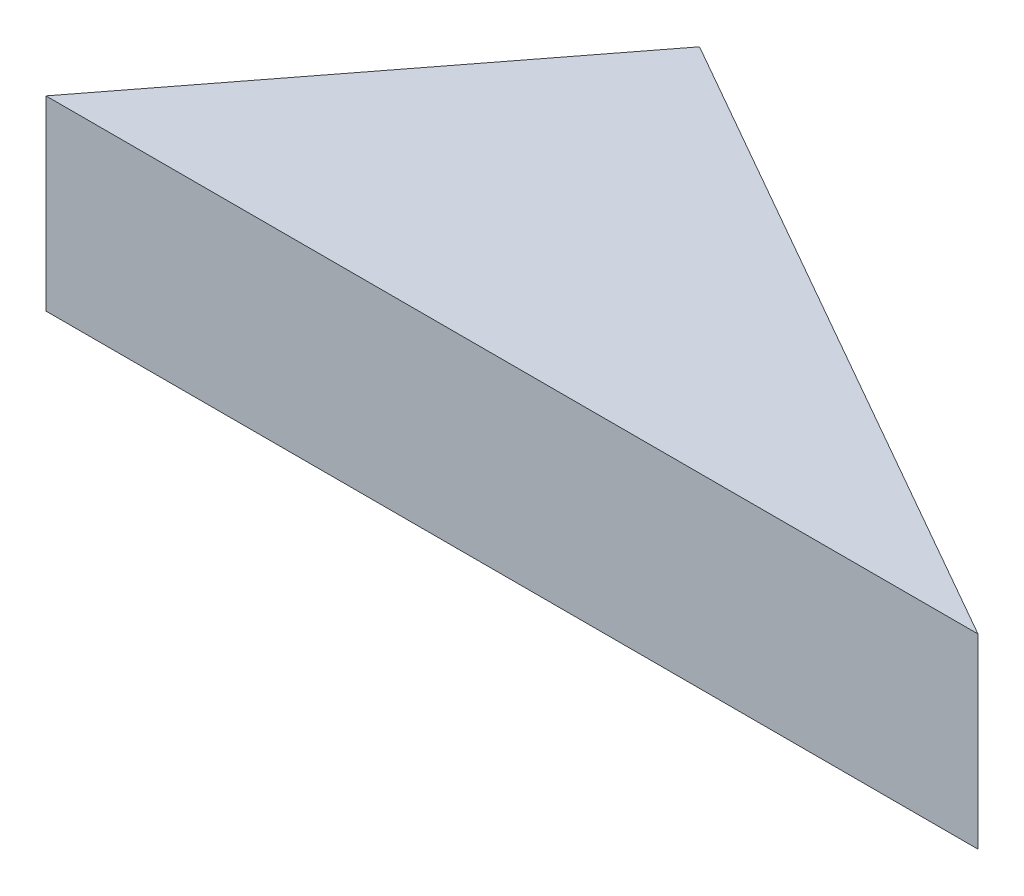
SolidWorks part; units mm, degrees
ref_plane "Front Plane" through (0, 0, 0) normal (0, 0, 1) x (1, 0, 0)
ref_plane "Top Plane" through (0, 0, 0) normal (0, 1, 0) x (1, 0, 0)
ref_plane "Right Plane" through (0, 0, 0) normal (1, 0, 0) x (0, 0, -1)
sketch "Sketch2" plane through (0, 0, 0) normal (0, 1, 0) x (1, 0, 0)
  line L0 (0, 0) -> (5, 0)
  line L1 (5, 0) -> (1.525, 1.981)
  line L2 (1.525, 1.981) -> (0, 0)
  dimension "D1" = 5
  dimension "D2" = 4
  dimension "D3" = 2.5
extrude "Boss-Extrude1" add sketch "Sketch2" along normal blind 1
equation "\"A\"= 5mm"
equation "\"B\"= 4mm"
equation "\"C\"= \"A\" - \"B\""
equation "\"D1@Sketch2\"=\"A\""
equation "\"D2@Sketch2\"=\"B\""
equation "\"D3@Sketch2\"=\"A\"/2"
equation "\"D1@Boss-Extrude1\"=\"C\""
